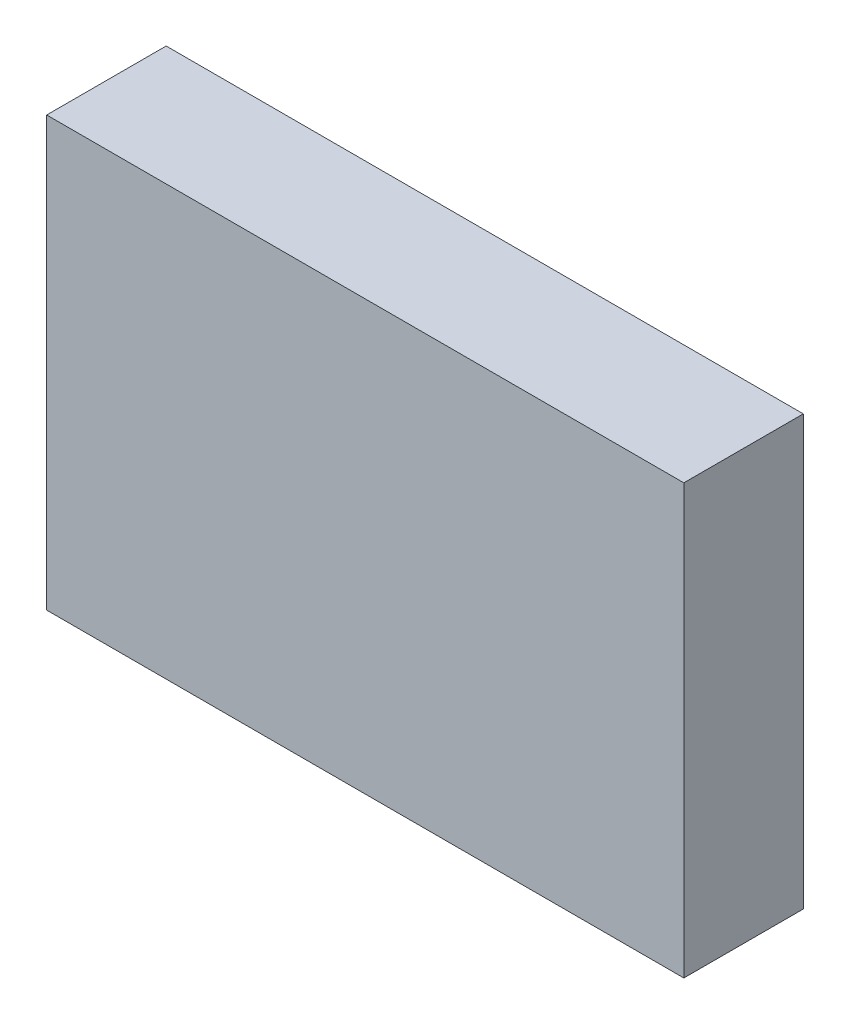
SolidWorks part; units mm, degrees
ref_plane "前视基准面" through (0, 0, 0) normal (0, 0, 1) x (1, 0, 0)
ref_plane "上视基准面" through (0, 0, 0) normal (0, 1, 0) x (1, 0, 0)
ref_plane "右视基准面" through (0, 0, 0) normal (1, 0, 0) x (0, 0, -1)
sketch "草图1" plane through (0, 0, 0) normal (0, 0, 1) x (1, 0, 0)
  line L1 (260, -175) -> (-260, -175)
  line L2 (260, -175) -> (260, 175)
  line L3 (260, 175) -> (-260, 175)
  line L4 (-260, -175) -> (-260, 175)
  line L5 (260, -175) -> (-260, 175) construction
  line L6 (260, 175) -> (-260, -175) construction
  point P0 (0, 0)
  dimension "D1" = 350
  dimension "D2" = 520
extrude "凸台-拉伸1" add sketch "草图1" along normal blind 97.5
